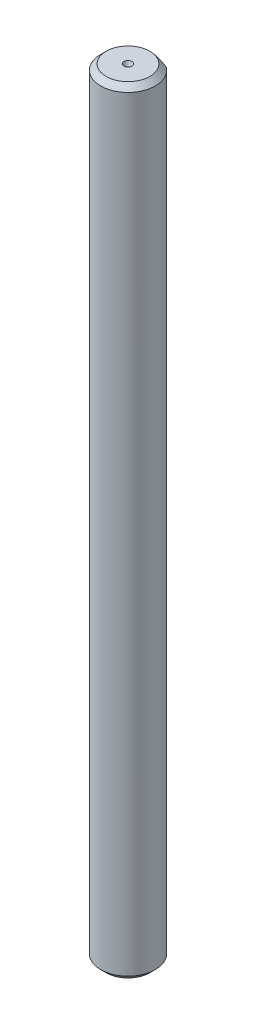
SolidWorks part; units mm, degrees
ref_plane "Спереди" through (0, 0, 0) normal (0, 0, 1) x (1, 0, 0)
ref_plane "Сверху" through (0, 0, 0) normal (0, 1, 0) x (1, 0, 0)
ref_plane "Справа" through (0, 0, 0) normal (1, 0, 0) x (0, 0, -1)
sketch "Эскиз1" plane through (0, 0, 0) normal (0, 1, 0) x (1, 0, 0)
  circle A0 centre (0, 0) radius 2.5
extrude "Бобышка-Вытянуть1" add sketch "Эскиз1" along normal blind 71
chamfer "Фаска1" distance 0.5 angle 45 2 edges at (0, 0, 2.5) (0, 71, 2.5)
sketch "Эскиз2" plane through (0, 71, 0) normal (0, 1, 0) x (1, 0, 0)
  circle A0 centre (0, 0) radius 0.3689
extrude "Вырез-Вытянуть1" cut sketch "Эскиз2" against normal blind 1 draft 22
sketch "Эскиз3" plane through (0, 71, 0) normal (0, 1, 0) x (1, 0, 0)
  line L0 (-1.5, 2) -> (1.5, 2)
  line L1 (0, -2.5) -> (-2.7672, -2.5) construction
  arc A0 (1.5, 2) -> (-1.5, 2) centre (0, 0) ccw
  dimension "D1" = 4.5
extrude "Вырез-Вытянуть2" cut sketch "Эскиз3" against normal blind 15
